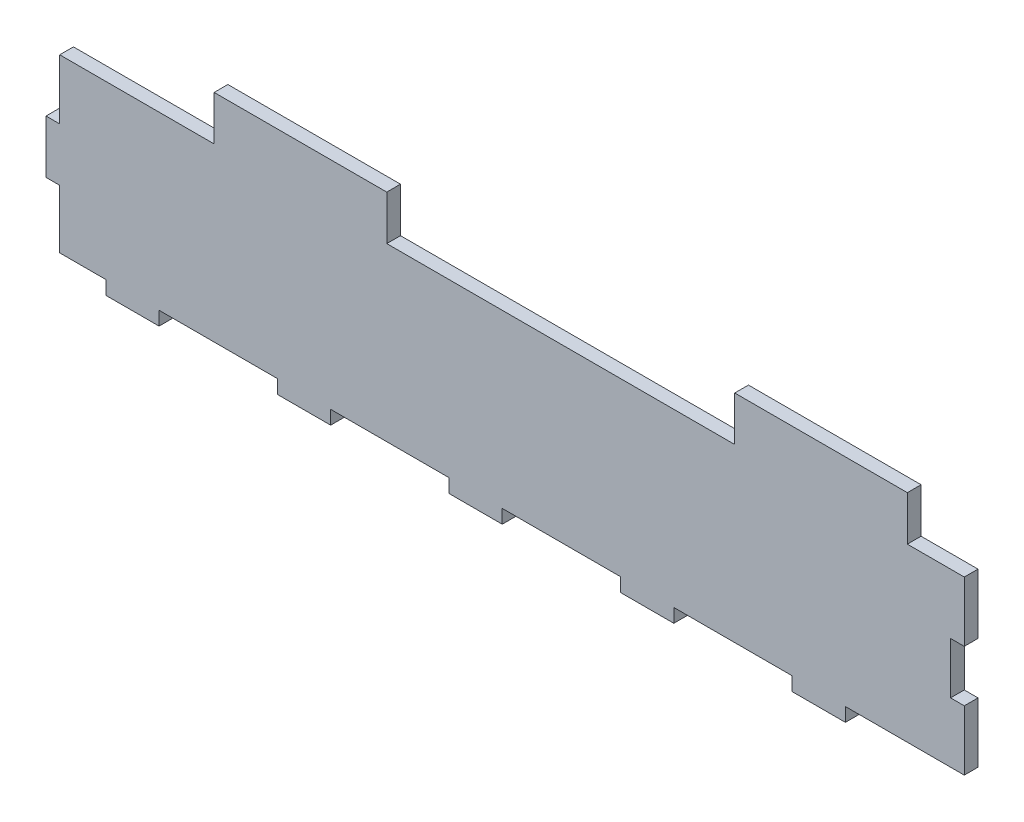
SolidWorks part; units mm, degrees
ref_plane "Ebene vorne" through (0, 0, 0) normal (0, 0, 1) x (1, 0, 0)
ref_plane "Ebene oben" through (0, 0, 0) normal (0, 1, 0) x (1, 0, 0)
ref_plane "Ebene rechts" through (0, 0, 0) normal (1, 0, 0) x (0, 0, -1)
sketch "Skizze1" plane through (0, 0, 0) normal (0, 0, 1) x (1, 0, 0)
  line L0 (0, 0) -> (0, 50)
  line L1 (0, 50) -> (300, 50)
  line L2 (300, 50) -> (300, 0)
  line L3 (300, 0) -> (0, 0)
  line L4 (40, 50) -> (40, 65)
  line L5 (40, 65) -> (80, 65)
  line L6 (80, 65) -> (80, 50)
  line L7 (80, 50) -> (40, 50)
  line L8 (150, 71.6451) -> (150, -46.4062) construction
  line L9 (220, 50) -> (260, 50)
  line L10 (220, 65) -> (220, 50)
  line L11 (260, 65) -> (220, 65)
  line L12 (260, 50) -> (260, 65)
  dimension "D1" = 50
  dimension "D2" = 300
  dimension "D3" = 40
  dimension "D4" = 40
  dimension "D5" = 15
extrude "Aufsatz-Linear austragen1" add sketch "Skizze1" along normal blind 4 contours L1 L2 L3 L0
sketch "Skizze2" plane through (0, 0, 0) normal (0, 0, 1) x (1, 0, 0)
  line L0 (300, 0) -> (0, 0) construction
  line L1 (17.45, 0) -> (32.95, 0)
  line L2 (17.45, 0) -> (17.45, -4)
  line L3 (17.45, -4) -> (32.95, -4)
  line L4 (32.95, 0) -> (32.95, -4)
  line L5 (0, 0) -> (0, 50) construction
  line L6 (67.45, 0) -> (82.95, 0)
  line L7 (67.45, 0) -> (67.45, -4)
  line L8 (67.45, -4) -> (82.95, -4)
  line L9 (82.95, 0) -> (82.95, -4)
  line L10 (117.45, 0) -> (132.95, 0)
  line L11 (117.45, 0) -> (117.45, -4)
  line L12 (117.45, -4) -> (132.95, -4)
  line L13 (132.95, 0) -> (132.95, -4)
  line L14 (167.45, 0) -> (182.95, 0)
  line L15 (167.45, 0) -> (167.45, -4)
  line L16 (167.45, -4) -> (182.95, -4)
  line L17 (182.95, 0) -> (182.95, -4)
  line L18 (217.45, 0) -> (232.95, 0)
  line L19 (217.45, 0) -> (217.45, -4)
  line L20 (217.45, -4) -> (232.95, -4)
  line L21 (232.95, 0) -> (232.95, -4)
  line L22 (267.45, 0) -> (282.95, 0)
  line L23 (267.45, 0) -> (267.45, -4)
  line L24 (267.45, -4) -> (282.95, -4)
  line L25 (282.95, 0) -> (282.95, -4)
  dimension "D1" = 4
  dimension "D2" = 15.5
  dimension "D3" = 17.45
extrude "Aufsatz-Linear austragen3" add sketch "Skizze2" along normal blind 4
sketch "Skizze3" plane through (0, 0, 4) normal (0, 0, 1) x (1, 0, 0)
  line L0 (17.45, 0) -> (0, 0) construction
  line L1 (0, 50) -> (4, 50)
  line L2 (0, 50) -> (0, 32.55)
  line L3 (0, 0) -> (4, 0)
  line L4 (4, 50) -> (4, 32.55)
  line L5 (0, 50) -> (300, 50) construction
  line L6 (0, 32.55) -> (4, 32.55)
  line L8 (0, 17.05) -> (4, 17.05)
  line L10 (0, 17.05) -> (0, 0)
  line L11 (4, 17.05) -> (4, 0)
  line L12 (150, 50) -> (150, -25.3923) construction
  line L24 (296, 17.05) -> (296, 0)
  line L25 (300, 17.05) -> (300, 0)
  line L26 (300, 17.05) -> (296, 17.05)
  line L27 (300, 32.55) -> (296, 32.55)
  line L28 (296, 50) -> (296, 32.55)
  line L29 (300, 0) -> (296, 0)
  line L30 (300, 50) -> (300, 32.55)
  line L31 (300, 50) -> (296, 50)
  dimension "D1" = 4
  dimension "D2" = 15.5
  dimension "D3" = 17.45
extrude "Schnitt-Linear austragen1" cut sketch "Skizze3" against normal up to next
sketch "Skizze4" plane through (0, 0, 4) normal (0, 0, 1) x (1, 0, 0)
  line L0 (49, 50) -> (49, 63)
  line L1 (4, 50) -> (296, 50) construction
  line L2 (49, 63) -> (99.3, 63)
  line L3 (99.3, 63) -> (99.3, 50)
  line L4 (99.3, 50) -> (49, 50)
  line L5 (4, 32.55) -> (4, 50) construction
  line L6 (150, 90.4729) -> (150, -49.3171) construction
  line L7 (296, 50) -> (296, 32.55) construction
  line L8 (200.7, 50) -> (251, 50)
  line L9 (200.7, 63) -> (200.7, 50)
  line L10 (251, 63) -> (200.7, 63)
  line L11 (251, 50) -> (251, 63)
  dimension "D1" = 45
  dimension "D2" = 50.3
  dimension "D3" = 13
extrude "Aufsatz-Linear austragen4" add sketch "Skizze4" against normal up to surface (4 mm away) up to face at (150.1333, 6.9556, 0)
sketch "Skizze5" plane through (0, 0, 0) normal (0, 0, -1) x (-1, 0, 0)
  line L0 (-267.5892, 50) -> (-267.5892, 32.5)
  line L1 (-251, 50) -> (-296, 50) construction
  line L3 (-331.2914, 25) -> (-198.2335, 25) construction
  line L4 (-260.1811, -8.9033) -> (-305.1184, -8.9033)
  line L5 (-305.1184, -8.9033) -> (-305.1184, 50)
  line L6 (-305.1184, 50) -> (-267.5892, 50)
  line L8 (-267.45, 0) -> (-232.95, 0) construction
  line L9 (-267.5892, 17.5) -> (-267.5892, 0)
  line L10 (-267.5892, 32.5) -> (-263.5892, 32.5)
  line L12 (-267.5892, 17.5) -> (-263.5892, 17.5)
  line L13 (-263.5892, 32.5) -> (-263.5892, 17.5)
  line L15 (-263.5892, -4) -> (-263.5892, 0) construction
  line L16 (-260.1811, 0) -> (-267.5892, 0)
  line L17 (-260.1811, 0) -> (-260.1811, -8.9033)
  dimension "D1" = 15
  dimension "D2" = 4
extrude "Schnitt-Linear austragen2" cut sketch "Skizze5" against normal up to next
